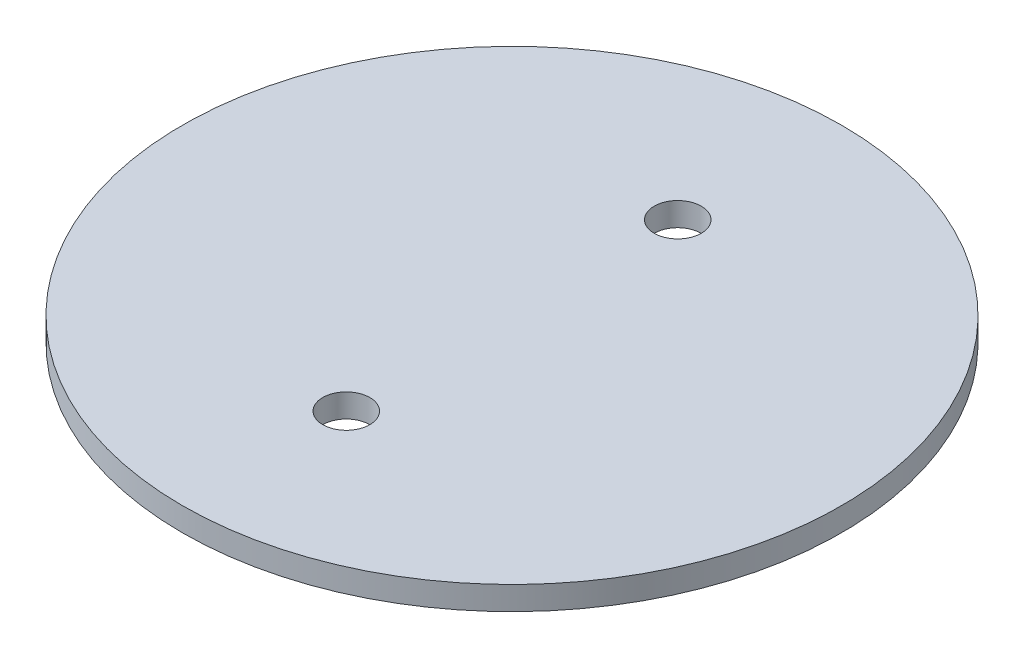
SolidWorks part; units mm, degrees
ref_plane "Front Plane" through (0, 0, 0) normal (0, 0, 1) x (1, 0, 0)
ref_plane "Top Plane" through (0, 0, 0) normal (0, 1, 0) x (1, 0, 0)
ref_plane "Right Plane" through (0, 0, 0) normal (1, 0, 0) x (0, 0, -1)
sketch "Sketch1" plane through (0, 0, 0) normal (0, 1, 0) x (1, 0, 0)
  line L0 (0, 0) -> (0, -22.352) construction
  line L1 (0, 0) -> (9.4568, 0)
  circle A0 centre (0, 0) radius 44.45
  circle A1 centre (0, -22.352) radius 3.175
  circle A2 centre (0, 22.352) radius 3.175
  point P9 (0, 0)
  point P10 (0, 0)
  dimension "D1" = 88.9
  dimension "D2" = 6.35
  dimension "D3" = 22.352
extrude "Boss-Extrude1" add sketch "Sketch1" along normal blind 3.175
